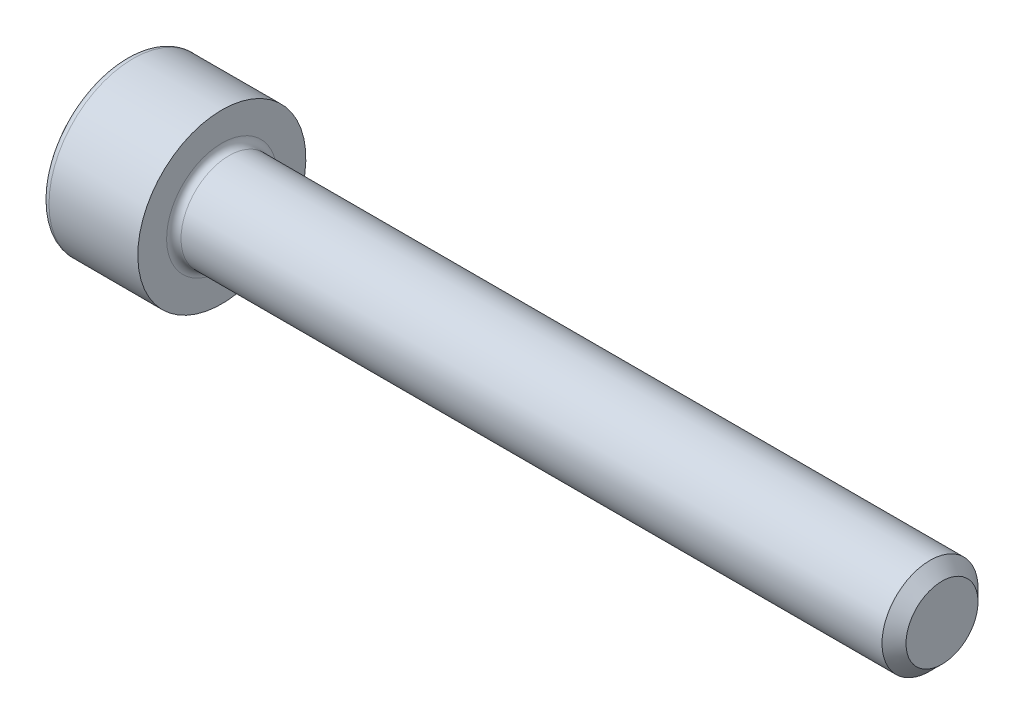
SolidWorks part; units mm, degrees
ref_plane "Спереди" through (0, 0, 0) normal (0, 0, 1) x (1, 0, 0)
ref_plane "Сверху" through (0, 0, 0) normal (0, 1, 0) x (1, 0, 0)
ref_plane "Справа" through (0, 0, 0) normal (1, 0, 0) x (0, 0, -1)
sketch "Эскиз1" plane through (0, 0, 0) normal (0, 0, 1) x (1, 0, 0)
  line L0 (0, 0) -> (0, 3.5)
  line L1 (0, 3.5) -> (4, 3.5)
  line L2 (4, 3.5) -> (4, 2)
  line L3 (4, 2) -> (34, 2)
  line L4 (34, 2) -> (34, 0)
  line L5 (34, 0) -> (0, 0) construction
  line L6 (0, 0) -> (34, 0)
  dimension "D1" = 7
  dimension "D2" = 4
  dimension "D3" = 4
  dimension "D4" = 30
revolve "Повернуть1" add sketch "Эскиз1" angle 360 about L5
cosmetic thread "Условное изображение резьбы1" parameters "D2"=3.22
sketch "Эскиз2" plane through (0, 0, 0) normal (-1, 0, 0) x (0, 0, 1)
  line L1 (-1.1547, 2) -> (-2.3094, 0)
  line L2 (-2.3094, 0) -> (-1.1547, -2)
  line L3 (-1.1547, -2) -> (1.1547, -2)
  line L4 (1.1547, -2) -> (2.3094, 0)
  line L5 (2.3094, 0) -> (1.1547, 2)
  line L6 (1.1547, 2) -> (-1.1547, 2)
  circle A0 centre (0, 0) radius 2 construction
  dimension "D1" = 4
extrude "Вырез-Вытянуть1" cut sketch "Эскиз2" against normal blind 2.5
fillet "Скругление1" radius 0.3 2 edges at (0, 3.5, 0) (4, 2, 0)
chamfer "Фаска1" distance 0.5 angle 45 1 edges at (34, 2, 0)
